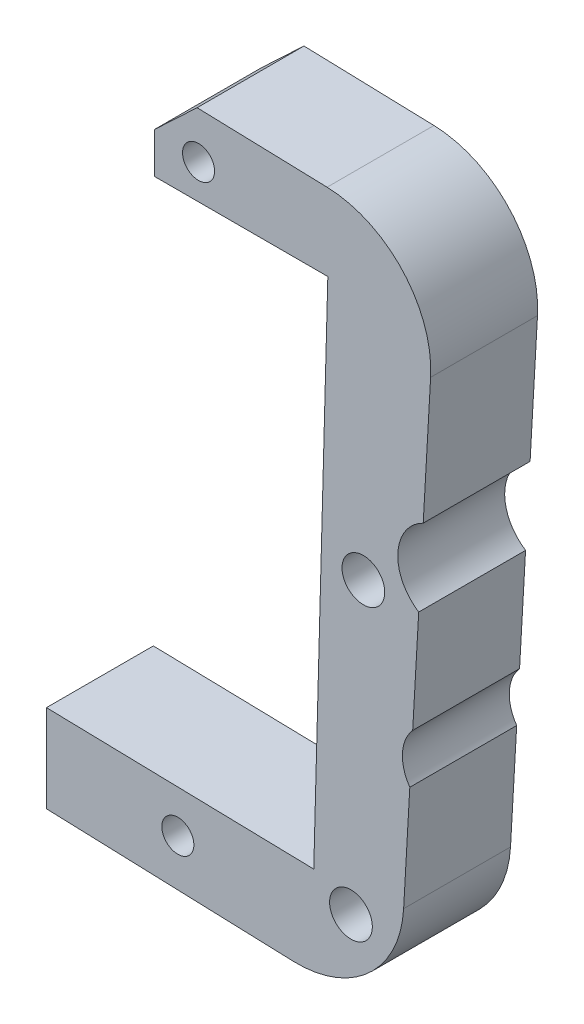
SolidWorks part; units mm, degrees
material "PMMA"
ref_plane "Front Plane" through (0, 0, 0) normal (0, 0, 1) x (1, 0, 0)
ref_plane "Top Plane" through (0, 0, 0) normal (0, 1, 0) x (1, 0, 0)
ref_plane "Right Plane" through (0, 0, 0) normal (1, 0, 0) x (0, 0, -1)
sketch "Sketch1" plane through (0, 0, 0) normal (0, 0, 1) x (1, 0, 0)
  line L0 (63.9786, 21.2146) -> (63.9786, 25.0559)
  line L1 (59.4897, 21.3185) -> (71.9944, 21.0289) construction
  line L2 (65.5716, 25.0002) -> (60.8745, 25.1643) construction
  line L3 (63.9786, 25.0559) -> (72.0583, 24.8167)
  line L4 (58.9304, -2.8329) -> (58.9304, -6.9332)
  line L5 (58.9304, -6.9332) -> (70.4738, -7.3363)
  line L6 (75.6402, -2.6236) -> (75.9286, 2.4403)
  line L7 (76.0637, 4.8116) -> (76.3447, 9.7463)
  line L8 (76.5559, 13.4539) -> (76.9022, 19.5346)
  line L9 (58.9304, -2.8329) -> (71.4351, -3.1225)
  line L10 (71.4351, -3.1225) -> (72.0935, 21.2146)
  line L11 (72.0204, 19.1216) -> (72.1879, 23.9187) construction
  line L12 (72.0935, 21.2146) -> (63.9786, 21.2146)
  arc A0 (75.6402, -2.6236) -> (70.4738, -7.3363) centre (70.6483, -2.3393) cw
  arc A1 (72.0583, 24.8167) -> (76.9022, 19.5346) centre (71.9103, 19.8189) cw
  arc A2 (76.0637, 4.8116) -> (75.9286, 2.4403) centre (77.5, 3.5403) ccw
  arc A3 (76.5559, 13.4539) -> (76.3447, 9.7463) centre (77.5, 11.5403) ccw
  circle A4 centre (73.1762, -4.0914) radius 1
  circle A5 centre (73.7561, 9.7463) radius 1
  point P17 (77.1944, 24.6647)
  point P33 (73.7561, 9.7463)
  dimension "D2" = 5
  dimension "D3" = 2
  dimension "D4" = 2
  dimension "D1" = 5.2
extrude "Boss-Extrude1" add sketch "Sketch1" along normal blind 5
sketch "Sketch2" plane through (0, 0, 5) normal (0, 0, 1) x (1, 0, 0)
  circle A0 centre (65.076, -4.9507) radius 0.75
  circle A1 centre (66.0463, 22.8323) radius 0.75
  dimension "D1" = 1.5
  dimension "D2" = 1.5
extrude "Cut-Extrude1" cut sketch "Sketch2" against normal blind 5
chamfer "Chamfer1" distance 2 angle 45 1 edges at (63.9786, 25.0559, 2.5)
